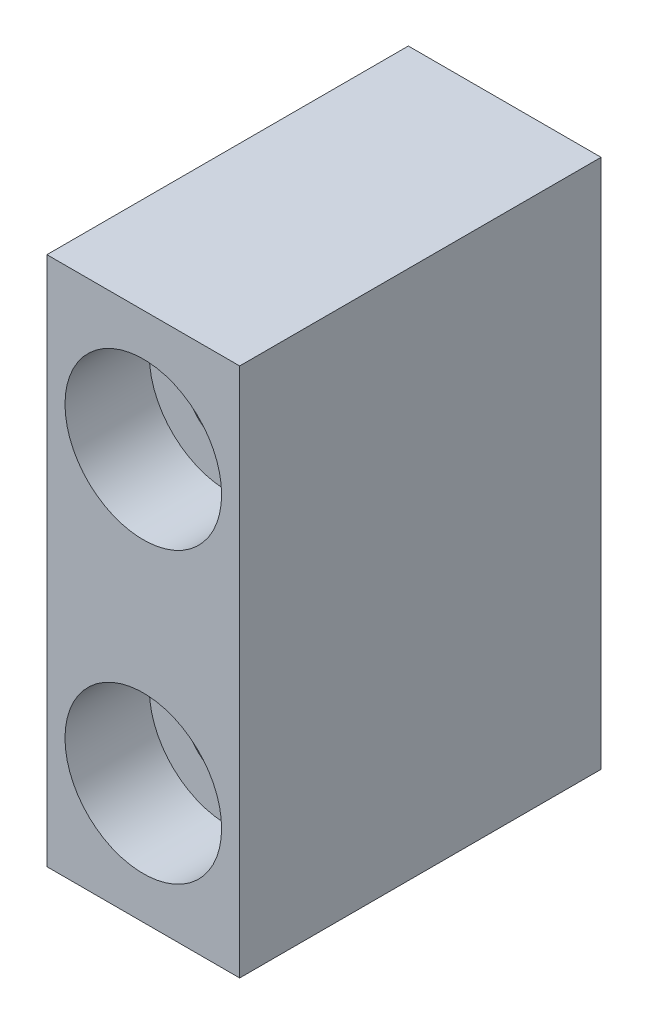
SolidWorks part; units mm, degrees
ref_plane "Front Plane" through (0, 0, 0) normal (0, 0, 1) x (1, 0, 0)
ref_plane "Top Plane" through (0, 0, 0) normal (0, 1, 0) x (1, 0, 0)
ref_plane "Right Plane" through (0, 0, 0) normal (1, 0, 0) x (0, 0, -1)
sketch "Sketch1" plane through (0, 0, 0) normal (0, 0, 1) x (1, 0, 0)
  line L1 (-8, 7.299) -> (0, 7.299)
  line L2 (-8, 7.299) -> (-8, -14.701)
  line L3 (-8, -14.701) -> (0, -14.701)
  line L4 (0, 7.299) -> (0, -14.701)
  dimension "D1" = 8
  dimension "D2" = 22
extrude "Boss-Extrude1" add sketch "Sketch1" along normal blind 15
sketch "Sketch2" plane through (0, 0, 15) normal (0, 0, 1) x (1, 0, 0)
  line L0 (0, 7.299) -> (-8, 7.299) construction
  line L1 (-8, -14.701) -> (0, -14.701) construction
  circle A0 centre (-4, 2.299) radius 1.75
  circle A1 centre (-4, -9.701) radius 1.75
  point P6 (-4, 7.299)
  point P9 (-4, -14.701)
  point P10 (0, 0)
  point P12 (-3.9414, -10.8602)
  dimension "D3" = 3.5
  dimension "D1" = 12
  dimension "D2" = 5
extrude "Cut-Extrude1" cut sketch "Sketch2" against normal through all
sketch "Sketch3" plane through (0, 0, 15) normal (0, 0, 1) x (1, 0, 0)
  circle A0 centre (-4, 2.299) radius 3.25
  circle A1 centre (-4, -9.701) radius 3.25
  dimension "D1" = 6.5
extrude "Cut-Extrude2" cut sketch "Sketch3" against normal blind 3.5
